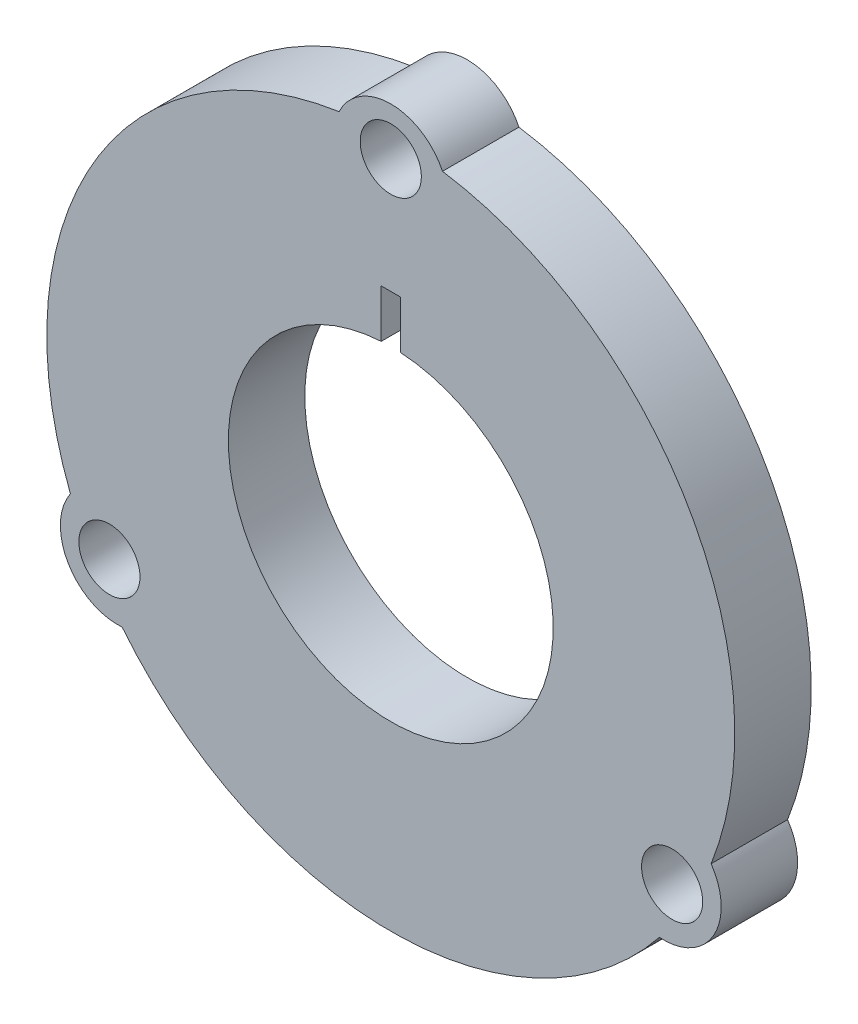
SolidWorks part; units mm, degrees
ref_plane "前视基准面" through (0, 0, 0) normal (0, 0, 1) x (1, 0, 0)
ref_plane "上视基准面" through (0, 0, 0) normal (0, 1, 0) x (1, 0, 0)
ref_plane "右视基准面" through (0, 0, 0) normal (1, 0, 0) x (0, 0, -1)
sketch "草图1" plane through (0, 0, 0) normal (0, 0, 1) x (1, 0, 0)
  circle A0 centre (0, 0) radius 8.5
  arc A1 (-14.0584, -11.2411) -> (14.0584, -11.2411) centre (0, 0) ccw
  circle A2 centre (0, 0) radius 16.5 construction
  arc A3 (2.7059, 17.7955) -> (-2.7059, 17.7955) centre (0, 16.5) ccw
  arc A4 (14.0584, -11.2411) -> (16.7643, -6.5544) centre (14.2894, -8.25) ccw
  arc A5 (-16.7643, -6.5544) -> (-14.0584, -11.2411) centre (-14.2894, -8.25) ccw
  arc A6 (16.7643, -6.5544) -> (2.7059, 17.7955) centre (0, 0) ccw
  arc A7 (-2.7059, 17.7955) -> (-16.7643, -6.5544) centre (0, 0) ccw
  point P14 (0, 0)
  dimension "D1" = 3
extrude "凸台-拉伸1" add sketch "草图1" along normal blind 4
sketch "草图2" plane through (0, 0, 4) normal (0, 0, 1) x (1, 0, 0)
  circle A0 centre (0, 0) radius 17 construction
  circle A1 centre (0, 17) radius 1.6
  circle A2 centre (14.7224, -8.5) radius 1.6
  circle A3 centre (-14.7224, -8.5) radius 1.6
  point P12 (0, 0)
extrude "切除-拉伸1" cut sketch "草图2" against normal blind 10
sketch "草图3" plane through (0, 0, 0) normal (0, 0, -1) x (-1, 0, 0)
  line L0 (0, 0) -> (0.5, 0)
  line L1 (0.5, 0) -> (0.5, 11)
  line L2 (0.5, 11) -> (-0.5, 11)
  line L3 (-0.5, 11) -> (-0.5, 0)
  circle M14 centre (0, 0) radius 8.5
extrude "切除-拉伸3" cut sketch "草图3" against normal blind 4 and the other way through all contours L2 L3 L1 M14
